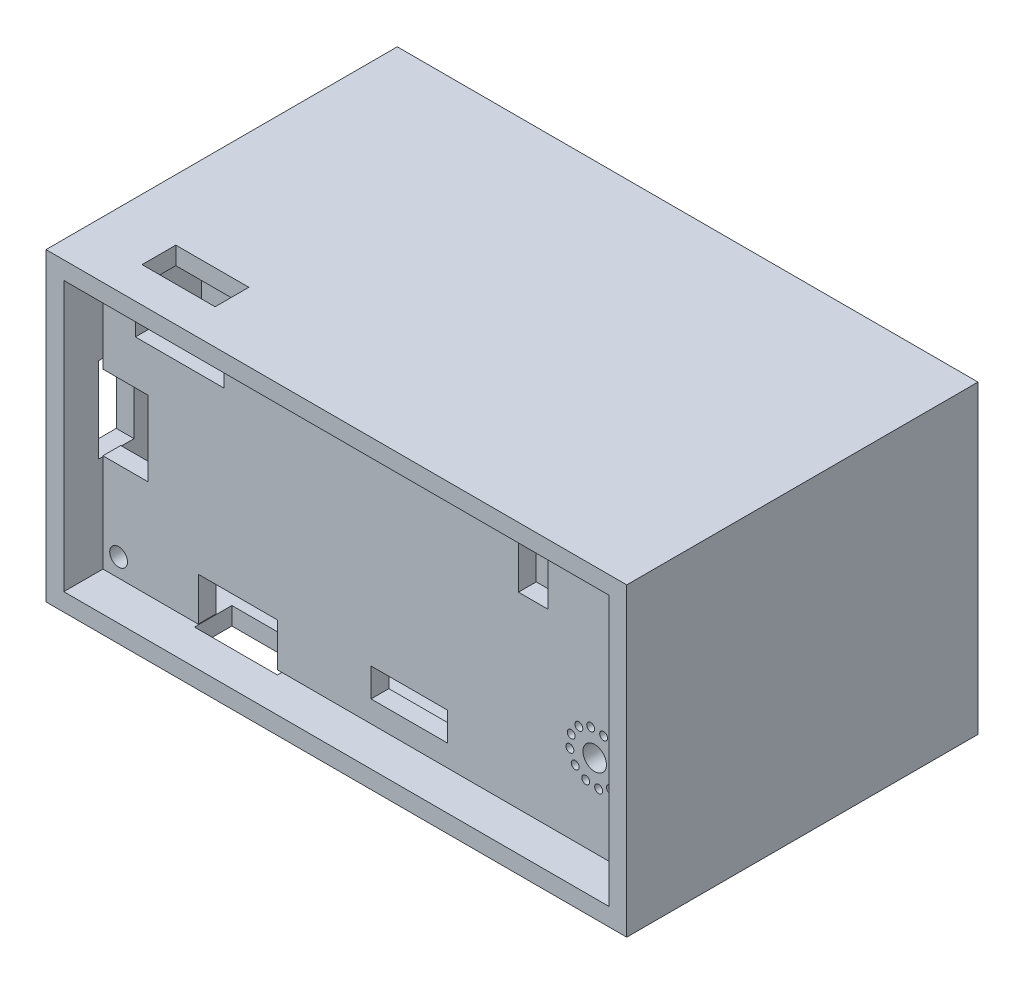
SolidWorks part; units mm, degrees
ref_plane "前视基准面" through (0, 0, 0) normal (0, 0, 1) x (1, 0, 0)
ref_plane "上视基准面" through (0, 0, 0) normal (0, 1, 0) x (1, 0, 0)
ref_plane "右视基准面" through (0, 0, 0) normal (1, 0, 0) x (0, 0, -1)
ref_plane "基准面1" through (0, 0, 3.6001) normal (0, 0, 1) x (1, 0, 0)
sketch "草图1" plane through (0, 0, 3.6001) normal (0, 0, 1) x (1, 0, 0)
  line L0 (0.8763, -38.7224) -> (-59.4234, -38.7224) construction
  line L1 (-48.7034, -33.8618) -> (-39.801, -33.8618)
  line L2 (-48.7034, -33.8618) -> (-48.7034, -38.7224)
  line L4 (-39.801, -33.8618) -> (-39.801, -38.7224)
  line L5 (-59.4234, -9.4107) -> (0.8763, -9.4107) construction
  line L7 (-55.7687, -9.4107) -> (-55.7687, -14.2907)
  line L8 (-55.7687, -14.2907) -> (-45.8066, -14.2907)
  line L9 (-45.8066, -9.4107) -> (-45.8066, -14.2907)
  line L10 (-12.699, -17.609) -> (-12.699, -12.109) construction
  line L11 (0.8763, -9.4107) -> (-45.8066, -9.4107)
  line L12 (0.8763, -9.4107) -> (0.8763, -38.7224)
  line L13 (0.8763, -38.7224) -> (-39.801, -38.7224)
  line L14 (-59.4234, -9.4107) -> (-59.4234, -19.2521)
  line L15 (-29.2736, -33.0846) -> (-20.6538, -33.0846)
  line L16 (-29.2736, -33.0846) -> (-29.2736, -36.2921)
  line L17 (-29.2736, -36.2921) -> (-20.6538, -36.2921)
  line L18 (-20.6538, -33.0846) -> (-20.6538, -36.2921)
  line L23 (-12.699, -12.109) -> (-9.399, -12.109)
  line L24 (-12.699, -12.109) -> (-12.699, -17.609)
  line L25 (-12.699, -17.609) -> (-9.399, -17.609)
  line L26 (-9.399, -12.109) -> (-9.399, -17.609)
  line L27 (-48.7034, -38.7224) -> (-59.4234, -38.7224)
  line L28 (-55.7687, -9.4107) -> (-59.4234, -9.4107)
  line L29 (-59.4234, -27.6866) -> (-59.4234, -38.7224)
  line L30 (-59.4234, -19.2521) -> (-54.3557, -19.2521)
  line L32 (-59.4234, -27.6866) -> (-54.3557, -27.6866)
  line L33 (-54.3557, -19.2521) -> (-54.3557, -27.6866)
  circle A0 centre (-57.6581, -36.6498) radius 1
  circle A1 centre (-57.6581, -11.2498) radius 1
  circle A2 centre (-1.016, -11.2498) radius 1
  circle A3 centre (-0.889, -36.8301) radius 1
  circle A4 centre (-4.1259, -29.4689) radius 1.322
  circle A5 centre (-5.9082, -27.2775) radius 0.4462
  circle A6 centre (-4.5737, -26.6799) radius 0.4462
  circle A7 centre (-3.1192, -26.8297) radius 0.4462
  circle A8 centre (-1.9345, -27.6866) radius 0.4462
  circle A9 centre (-1.3369, -29.0211) radius 0.4462
  circle A10 centre (-1.4866, -30.4756) radius 0.4462
  circle A11 centre (-2.3435, -31.6603) radius 0.4462
  circle A12 centre (-3.678, -32.2579) radius 0.4462
  circle A13 centre (-5.1325, -32.1082) radius 0.4462
  circle A14 centre (-6.3173, -31.2513) radius 0.4462
  circle A15 centre (-6.9149, -29.9168) radius 0.4462
  circle A16 centre (-6.7652, -28.4623) radius 0.4462
  point P71 (-4.1259, -29.4689)
  dimension "D1" = 12
extrude "凸台-拉伸1" add sketch "草图1" along normal blind 2
ref_plane "基准面2" through (0, 0, -6) normal (0, 0, -1) x (-1, 0, 0)
sketch "草图2" plane through (0, 0, -6) normal (0, 0, -1) x (-1, 0, 0)
  line L0 (29.2736, -9.4107) -> (29.2736, -29.309) construction
  line L1 (-0.8763, -38.7224) -> (59.4234, -38.7224)
  line L2 (-0.8763, -38.7224) -> (-0.8763, -9.4107)
  line L3 (-0.8763, -9.4107) -> (59.4234, -9.4107)
  line L4 (59.4234, -38.7224) -> (59.4234, -9.4107)
  line L5 (59.4234, -24.0665) -> (-9.3078, -24.0665) construction
  line L9 (29.2736, -15.8165) -> (29.2736, -13.1836) construction
  line L10 (27.7854, -15.8165) -> (27.7854, -13.1836)
  line L11 (30.7617, -15.8165) -> (30.7617, -13.1836)
  line L12 (29.2736, -38.7224) -> (29.2736, -43.3487) construction
  line L14 (-3.3763, -6.9107) -> (61.9234, -6.9107)
  line L15 (-3.3763, -6.9107) -> (-3.3763, -41.2224)
  line L16 (-3.3763, -41.2224) -> (61.9234, -41.2224)
  line L17 (61.9234, -6.9107) -> (61.9234, -41.2224)
  circle A0 centre (1.016, -11.2498) radius 1
  circle A1 centre (0.889, -36.8301) radius 1
  circle A2 centre (57.6581, -36.6498) radius 1
  circle A3 centre (57.6581, -11.2498) radius 0.9222
  arc A10 (27.7854, -15.8165) -> (30.7617, -15.8165) centre (29.2736, -15.8165) ccw
  arc A11 (30.7617, -13.1836) -> (27.7854, -13.1836) centre (29.2736, -13.1836) ccw
  circle A12 centre (29.2736, -32.3165) radius 1.5
  point P27 (29.2736, -31.5665)
  point P33 (29.2736, -14.5001)
  dimension "D1" = 2.5
  dimension "D2" = 2.5
  dimension "D3" = 3
  dimension "D4" = 8.25
  dimension "D5" = 2.5
  dimension "D6" = 2.5
  dimension "D7" = 8.25
extrude "凸台-拉伸2" add sketch "草图2" along normal blind 4.5 separate body
sketch "草图3" plane through (0, 0, -6) normal (0, 0, -1) x (-1, 0, 0)
  line L0 (29.2736, -15.8165) -> (29.2736, -10.8487) construction
  line L1 (32.0236, -17.4043) -> (32.0236, -14.2288)
  line L4 (26.5236, -14.2288) -> (26.5236, -17.4043)
  line L5 (26.5236, -17.4043) -> (29.2736, -18.992)
  line L6 (29.2736, -18.992) -> (32.0236, -17.4043)
  line L8 (32.0236, -14.9203) -> (32.0236, -11.7449)
  line L9 (32.0236, -11.7449) -> (29.2736, -10.1572)
  line L10 (29.2736, -10.1572) -> (26.5236, -11.7449)
  line L11 (26.5236, -11.7449) -> (26.5236, -14.9203)
  line L14 (31.8974, -14.9932) -> (32.0236, -14.9203) [skipped]
  line L15 (29.2736, -22.4541) -> (17.663, -22.4541) construction
  line L16 (29.2736, -22.4541) -> (29.2736, -17.3047) construction
  line L17 (26.6497, -14.156) -> (26.5236, -14.2288) [skipped]
  line L18 (26.5236, -14.9203) -> (26.6497, -14.9932) [skipped]
  line L19 (32.0236, -14.2288) -> (31.8974, -14.156) [skipped]
  line L20 (26.5236, -33.9043) -> (29.2736, -35.492)
  line L21 (29.2736, -35.492) -> (32.0236, -33.9043)
  line L22 (32.0236, -33.9043) -> (32.0236, -30.7288)
  line L23 (32.0236, -30.7288) -> (29.2736, -29.1411)
  line L24 (29.2736, -29.1411) -> (26.5236, -30.7288)
  line L25 (26.5236, -30.7288) -> (26.5236, -33.9043)
  arc A0 (26.82, -14.5746) -> (31.7271, -14.5746) centre (29.2736, -15.8165) ccw construction
  arc A1 (31.7271, -14.5746) -> (26.82, -14.5746) centre (29.2736, -13.3326) ccw construction
  circle A2 centre (29.2736, -32.3165) radius 2.75 construction
  arc A5 (27.7854, -15.8165) -> (30.7617, -15.8165) centre (29.2736, -15.8165) ccw construction
  point P25 (29.2736, -33.8241)
  dimension "D1" = 5.5
extrude "切除-拉伸2" cut sketch "草图3" along normal blind 2.5 contours L10 L11 L4 L5 L6 L1 L8 L9 | L24 L25 L20 L21 L22 L23
sketch "草图5" plane through (0, 0, -10.5) normal (0, 0, -1) x (-1, 0, 0)
  line L1 (-3.3763, -6.9107) -> (61.9234, -6.9107)
  line L2 (-3.3763, -6.9107) -> (-3.3763, -41.2224)
  line L3 (-3.3763, -41.2224) -> (61.9234, -41.2224)
  line L4 (61.9234, -6.9107) -> (61.9234, -41.2224)
  line L5 (-1.3763, -8.9107) -> (59.9234, -8.9107)
  line L6 (-1.3763, -8.9107) -> (-1.3763, -39.2224)
  line L7 (-1.3763, -39.2224) -> (59.9234, -39.2224)
  line L8 (59.9234, -8.9107) -> (59.9234, -39.2224)
  dimension "D1" = 2
  dimension "D2" = 2
  dimension "D3" = 2
  dimension "D4" = 2
extrude "凸台-拉伸3" add sketch "草图5" along normal blind 15.5 and the other way blind 20
sketch "草图7" plane through (0, -6.9107, 0) normal (0, 1, 0) x (1, 0, 0)
  line L0 (-41.7981, -5.5601) -> (-46.8481, -5.5601) construction
  line L1 (-55.0622, -1.765) -> (-46.8481, -1.765)
  line L2 (-55.0622, -1.765) -> (-55.0622, -5.5601)
  line L3 (-55.0622, -5.5601) -> (-46.8481, -5.5601)
  line L4 (-46.8481, -1.765) -> (-46.8481, -5.5601)
extrude "切除-拉伸4" cut sketch "草图7" against normal blind 3
sketch "草图8" plane through (-61.9234, 0, 0) normal (-1, 0, 0) x (0, 0, 1)
  line L0 (5.6001, -27.6866) -> (5.6001, -38.7224) construction
  line L1 (1.6001, -18.6953) -> (5.6001, -18.6953)
  line L2 (1.6001, -18.6953) -> (1.6001, -28.2708)
  line L3 (1.6001, -28.2708) -> (5.6001, -28.2708)
  line L4 (5.6001, -18.6953) -> (5.6001, -28.2708)
  dimension "D1" = 4
extrude "切除-拉伸5" cut sketch "草图8" against normal blind 3
sketch "草图9" plane through (0, -41.2224, 0) normal (0, -1, 0) x (1, 0, 0)
  line L0 (-59.4234, 5.6001) -> (-48.7034, 5.6001) construction
  line L1 (-49.1273, 5.6001) -> (-39.801, 5.6001)
  line L2 (-49.1273, 5.6001) -> (-49.1273, 1.3978)
  line L3 (-49.1273, 1.3978) -> (-39.801, 1.3978)
  line L4 (-39.801, 5.6001) -> (-39.801, 1.3978)
extrude "切除-拉伸6" cut sketch "草图9" against normal blind 3
sketch "草图10" plane through (0, 0, -26) normal (0, 0, -1) x (-1, 0, 0)
  line L0 (29.2736, -8.9107) -> (29.2736, -43.7563) construction
  line L1 (-3.3763, -6.9107) -> (61.9234, -6.9107)
  line L2 (-3.3763, -6.9107) -> (-3.3763, -41.2224)
  line L3 (-3.3763, -41.2224) -> (61.9234, -41.2224)
  line L4 (61.9234, -6.9107) -> (61.9234, -41.2224)
  line L5 (-1.3763, -8.9107) -> (59.9234, -8.9107)
  line L6 (-1.3763, -8.9107) -> (-1.3763, -39.2224)
  line L7 (-1.3763, -39.2224) -> (59.9234, -39.2224)
  line L8 (59.9234, -8.9107) -> (59.9234, -39.2224)
  line L9 (-1.3763, -24.0665) -> (74.3166, -24.0665) construction
  circle A0 centre (1.016, -11.2498) radius 1
  arc A1 (-1.3763, -14.9107) -> (4.6237, -8.9107) centre (-1.3763, -8.9107) ccw
  circle A2 centre (57.6581, -11.2498) radius 1
  arc A3 (53.9234, -8.9107) -> (59.9234, -14.9107) centre (59.9234, -8.9107) ccw
  circle A4 centre (57.6581, -36.8833) radius 1
  arc A5 (53.9234, -39.2224) -> (59.9234, -33.2224) centre (59.9234, -39.2224) cw
  circle A6 centre (1.016, -36.8833) radius 1
  arc A7 (-1.3763, -33.2224) -> (4.6237, -39.2224) centre (-1.3763, -39.2224) cw
  line M2 (-3.3763, -6.9107) -> (-3.3763, -41.2224)
  line M3 (-3.3763, -41.2224) -> (61.9234, -41.2224)
  line M4 (61.9234, -41.2224) -> (61.9234, -6.9107)
  line M5 (61.9234, -6.9107) -> (-3.3763, -6.9107)
  line M6 (59.9234, -39.2224) -> (-1.3763, -39.2224)
  line M7 (-1.3763, -39.2224) -> (-1.3763, -8.9107)
  line M8 (-1.3763, -8.9107) -> (59.9234, -8.9107)
  line M9 (59.9234, -8.9107) -> (59.9234, -39.2224)
  dimension "D1" = 6
  dimension "D2" = 6
  dimension "D3" = 2
  dimension "D4" = 2
extrude "凸台-拉伸4" add sketch "草图10" along normal blind 4 contours L8 L7 L6 L5 M5 M2 M3 M4 M9 M6 M7 M8 | L6 A1 A0 M8 | A7 A6 M7 M6 | A5 A4 M6 M9 | A3 A2 M8 M9
sketch "草图11" plane through (0, 0, -30) normal (0, 0, -1) x (-1, 0, 0)
  line L1 (-3.3763, -6.9107) -> (61.9234, -6.9107)
  line L2 (-3.3763, -6.9107) -> (-3.3763, -41.2224)
  line L3 (-3.3763, -41.2224) -> (61.9234, -41.2224)
  line L4 (61.9234, -6.9107) -> (61.9234, -41.2224)
  circle A0 centre (1.016, -11.2498) radius 1
  circle A1 centre (1.016, -36.8833) radius 1
  circle A2 centre (57.6581, -36.8833) radius 1
  circle A3 centre (57.6581, -11.2498) radius 1
